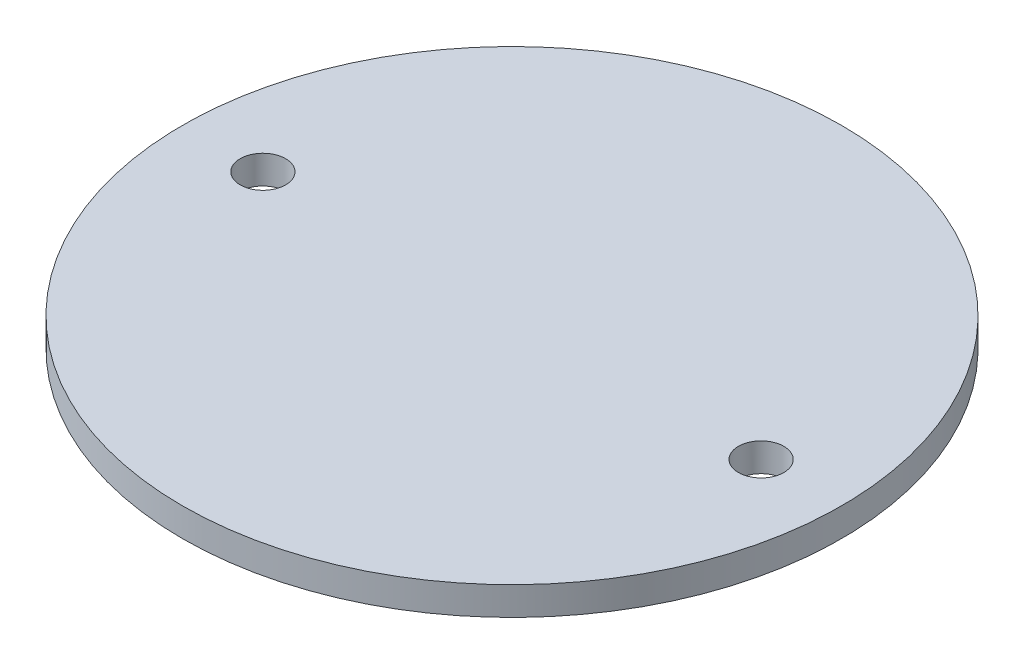
SolidWorks part; units mm, degrees
ref_plane "Front Plane" through (0, 0, 0) normal (0, 0, 1) x (1, 0, 0)
ref_plane "Top Plane" through (0, 0, 0) normal (0, 1, 0) x (1, 0, 0)
ref_plane "Right Plane" through (0, 0, 0) normal (1, 0, 0) x (0, 0, -1)
sketch "Sketch1" plane through (0, 0, 0) normal (0, 1, 0) x (1, 0, 0)
  circle A0 centre (0, 0) radius 73.66
  dimension "D1" = 147.32
extrude "Boss-Extrude1" add sketch "Sketch1" along normal blind 6.35
sketch "Sketch2" plane through (0, 0, 0) normal (0, 1, 0) x (1, 0, 0)
  line L0 (0, 73.66) -> (0, -73.66) construction
  circle A0 centre (0, 0) radius 73.66 construction
  circle A1 centre (-55.6787, 0) radius 5.08
  circle A2 centre (55.6787, 0) radius 5.08
extrude "Cut-Extrude1" cut sketch "Sketch2" against normal through all both and the other way through all
